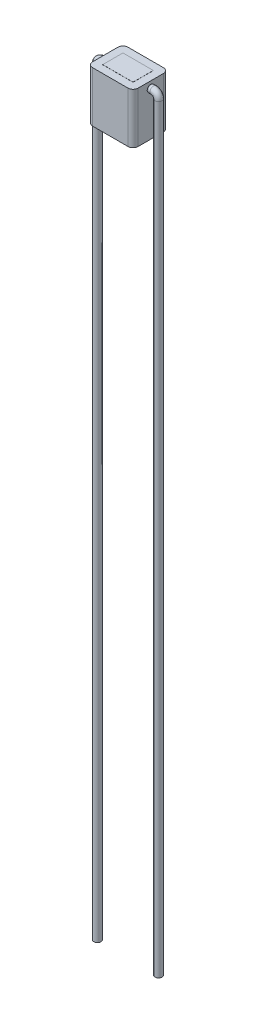
SolidWorks part; units mm, degrees
ref_plane "Front Plane" through (0, 0, 0) normal (0, 0, 1) x (1, 0, 0)
ref_plane "Top Plane" through (0, 0, 0) normal (0, 1, 0) x (1, 0, 0)
ref_plane "Right Plane" through (0, 0, 0) normal (1, 0, 0) x (0, 0, -1)
sketch "Sketch1" plane through (0, 0, 0) normal (0, 1, 0) x (1, 0, 0)
  line L1 (-2.25, 1.75) -> (2.25, 1.75)
  line L2 (-2.25, 1.75) -> (-2.25, -1.75)
  line L3 (-2.25, -1.75) -> (2.25, -1.75)
  line L4 (2.25, 1.75) -> (2.25, -1.75)
  line L5 (-2.25, 1.75) -> (2.25, -1.75) construction
  line L6 (-2.25, -1.75) -> (2.25, 1.75) construction
  point P0 (0, 0)
  dimension "D1" = 3.5
  dimension "D2" = 4.5
sketch "Sketch2" plane through (0, 0, 0) normal (0, 1, 0) x (1, 0, 0)
  line L1 (-1.5, 1) -> (1.5, 1)
  line L2 (-1.5, 1) -> (-1.5, -1)
  line L3 (-1.5, -1) -> (1.5, -1)
  line L4 (1.5, 1) -> (1.5, -1)
  line L5 (-1.5, 1) -> (1.5, -1) construction
  line L6 (-1.5, -1) -> (1.5, 1) construction
  point P0 (0, 0)
  dimension "D1" = 2
  dimension "D2" = 3
extrude "Boss-Extrude1" add sketch "Sketch1" along normal blind 5
extrude "Boss-Extrude2" add sketch "Sketch2" along normal blind 5.01 and the other way blind 0.01
fillet "Fillet2" radius 0.5 4 edges at (2.25, 2.5, 1.75) (-2.25, 2.5, 1.75) (-2.25, 2.5, -1.75) (2.25, 2.5, -1.75)
sketch "Sketch14" plane through (2.25, 0, 0) normal (1, 0, 0) x (0, 0, -1)
  circle A0 centre (0, 4.3538) radius 0.35
sketch "Sketch15" plane through (0, 0, 0) normal (0, 0, 1) x (1, 0, 0)
  line L0 (2.25, 4.3538) -> (2.3, 4.3538)
  line L1 (2.3, 4.3538) -> (2.5259, 4.3538)
  line L2 (3.0259, 3.8538) -> (3.0259, -71.1462)
  arc A0 (2.5259, 4.3538) -> (3.0259, 3.8538) centre (2.5259, 3.8538) cw
sweep "Sweep1" add profiles "Sketch14" path "Sketch15"
mirror "Mirror1" about plane through (0, 0, 0) normal (1, 0, 0) of "Sweep1"
